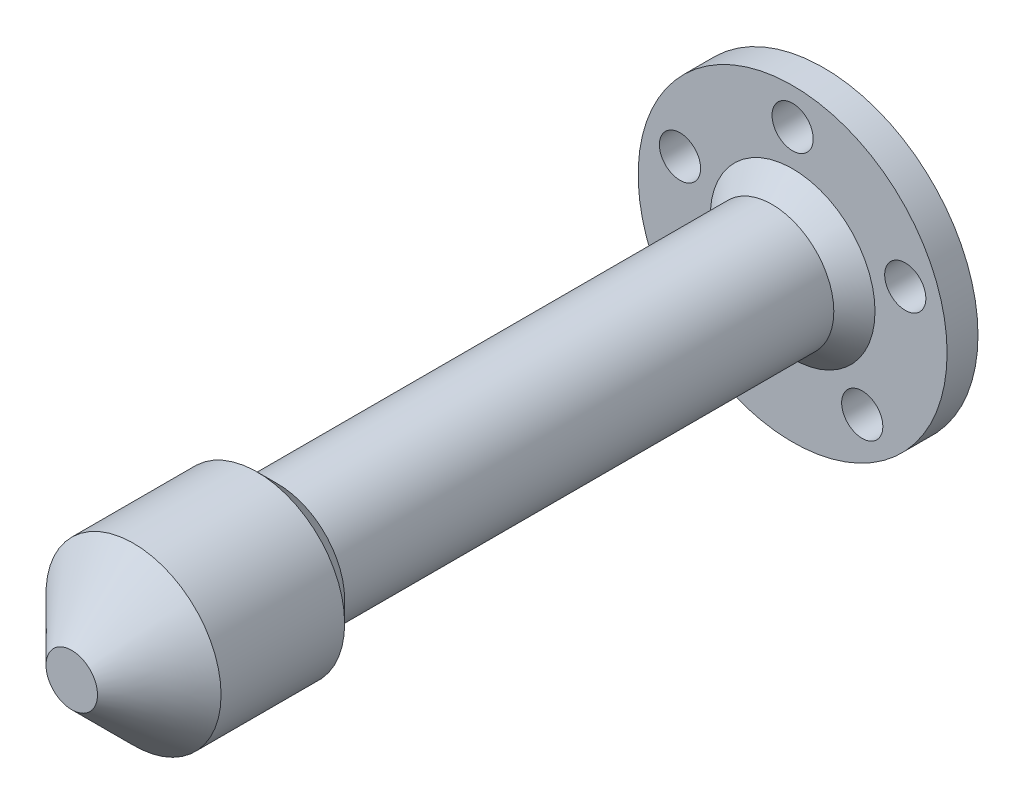
SolidWorks part; units mm, degrees
ref_plane "Front Plane" through (0, 0, 0) normal (0, 0, 1) x (1, 0, 0)
ref_plane "Top Plane" through (0, 0, 0) normal (0, 1, 0) x (1, 0, 0)
ref_plane "Right Plane" through (0, 0, 0) normal (1, 0, 0) x (0, 0, -1)
sketch "Sketch1" plane through (0, 0, 0) normal (0, 0, 1) x (1, 0, 0)
  circle A0 centre (0, 0) radius 15
  dimension "D1" = 30
extrude "Boss-Extrude1" add sketch "Sketch1" along normal blind 3
sketch "Sketch2" plane through (0, 0, 3) normal (0, 0, 1) x (1, 0, 0)
  circle A0 centre (0, 0) radius 11.5
  circle A1 centre (0, 11.5) radius 2
  circle A2 centre (10.9371, 3.5537) radius 2
  circle A3 centre (6.7595, -9.3037) radius 2
  circle A4 centre (-6.7595, -9.3037) radius 2
  circle A5 centre (-10.9371, 3.5537) radius 2
  point P15 (0, 0)
  dimension "D1" = 23
  dimension "D2" = 4
  dimension "D3" = 5
extrude "Cut-Extrude1" cut sketch "Sketch2" against normal blind 3 contours A1 | A5 | A4 | A3 | A2
sketch "Sketch3" plane through (0, 0, 3) normal (0, 0, 1) x (1, 0, 0)
  circle A0 centre (0, 0) radius 6
  dimension "D1" = 12
extrude "Boss-Extrude5" add sketch "Sketch3" along normal blind 50
chamfer "Chamfer1" distance 2 angle 45 1 edges at (6, 0, 3)
sketch "Sketch5" plane through (0, 0, 53) normal (0, 0, 1) x (1, 0, 0)
  circle A0 centre (0, 0) radius 8.5
  dimension "D1" = 17
extrude "Boss-Extrude6" add sketch "Sketch5" along normal blind 20
chamfer "Chamfer2" distance 6 angle 45 1 edges at (8.5, 0, 73)
chamfer "Chamfer3" distance 2 angle 45 1 edges at (8.5, 0, 53)
sketch "Sketch6" plane through (0, 0, 0) normal (0, 0, -1) x (-1, 0, 0)
  circle A0 centre (0, 0) radius 4.1
  dimension "D1" = 8.2
extrude "Cut-Extrude2" cut sketch "Sketch6" against normal blind 60
